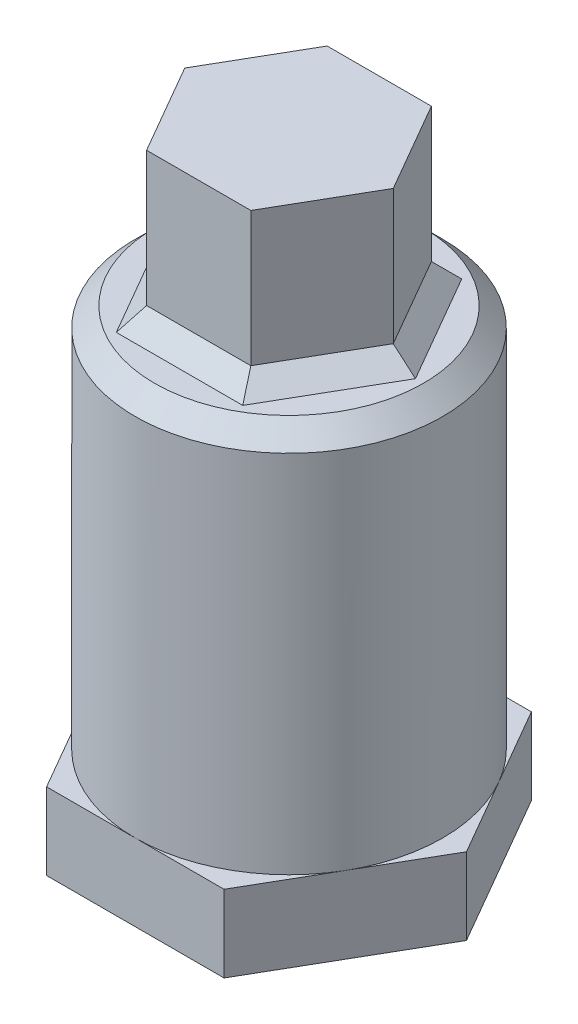
SolidWorks part; units mm, degrees
ref_plane "Front Plane" through (0, 0, 0) normal (0, 0, 1) x (1, 0, 0)
ref_plane "Top Plane" through (0, 0, 0) normal (0, 1, 0) x (1, 0, 0)
ref_plane "Right Plane" through (0, 0, 0) normal (1, 0, 0) x (0, 0, -1)
sketch "Sketch1" plane through (0, 0, 0) normal (0, 1, 0) x (1, 0, 0)
  line L1 (5.4271, 0) -> (2.7135, 4.7)
  line L2 (2.7135, 4.7) -> (-2.7135, 4.7)
  line L3 (-2.7135, 4.7) -> (-5.4271, 0)
  line L4 (-5.4271, 0) -> (-2.7135, -4.7)
  line L5 (-2.7135, -4.7) -> (2.7135, -4.7)
  line L6 (2.7135, -4.7) -> (5.4271, 0)
  circle A0 centre (0, 0) radius 4.7 construction
  dimension "D1" = 9.4
extrude "Boss-Extrude1" add sketch "Sketch1" along normal blind 8
sketch "Sketch2" plane through (0, 0, 0) normal (0, -1, 0) x (1, 0, 0)
  circle A0 centre (0, 0) radius 8
  dimension "D1" = 16
extrude "Boss-Extrude2" add sketch "Sketch2" along normal blind 20
chamfer "Chamfer1" distance 1 angle 45 7 edges at (0, 0, -8) (4.0703, 0, -2.35) (0, 0, -4.7) (-4.0703, 0, -2.35) (-4.0703, 0, 2.35) (0, 0, 4.7) (4.0703, 0, 2.35)
sketch "Sketch3" plane through (0, -20, 0) normal (0, -1, 0) x (1, 0, 0)
  circle A0 centre (0, 0) radius 23
  circle A1 centre (0, 0) radius 8 construction
  dimension "D1" = 15
extrude "Boss-Extrude3" add sketch "Sketch3" along normal blind 7
sketch "Sketch4" plane through (0, -27, 0) normal (0, -1, 0) x (1, 0, 0)
  line L1 (4.4, 0) -> (-4.4, 0) construction
  arc A0 (-24.8365, -2.8544) -> (-24.8365, 2.8544) centre (0, 0) cw construction
  arc A2 (-28.876, -2.6786) -> (-28.876, 2.6786) centre (0, 0) cw
  arc A3 (-28.8104, -3.3111) -> (-28.8104, 3.3111) centre (0, 0) cw construction
  spline S0 degree 3 poles (-28.876, 2.6786) (-27.341, 2.7837) (-21.4523, 3.0394) (-17.8705, 2.2022) (-15.9721, 0.5752) (-15.3766, 0) knots -0.203879 -0.203879 -0.203879 -0.203879 0 0.695602 1 1 1 1
  spline S1 degree 3 poles (-28.876, -2.6786) (-27.341, -2.7837) (-21.4523, -3.0394) (-17.8705, -2.2022) (-15.9721, -0.5752) (-15.3766, 0) knots -0.203879 -0.203879 -0.203879 -0.203879 0 0.695602 1 1 1 1
  point P11 (0, 0)
  dimension "D1" = 4
extrude "Cut-Extrude1" cut sketch "Sketch4" against normal blind 1 draft 45
fillet "Fillet2" radius 1 5 edges at (-22.8819, -26.5002, -2.3277) (-22.9013, -26.3001, 2.1282) (-23, -26, 0) (-18.9133, -26, 1.1779) (-21.1533, -26, -1.6856)
pattern_circular "CirPattern1" count 6 every 45 about axis through (0, -27, 0) along (0, 1, 0) of "Cut-Extrude1", "Fillet2"
sketch "Sketch5" plane through (0, -27, 0) normal (0, -1, 0) x (1, 0, 0)
  line L0 (-245.0554, -113.5226) -> (-245.0554, 81.9035) construction
  line L1 (0, -4.4) -> (0, 4.4) construction
  line L2 (-2.4074, -8.5668) -> (0, -10.6858)
  line L3 (0, 0.7457) -> (0, -10.6858) construction
  line L4 (2.4074, -8.5668) -> (0, -10.6858)
  spline S0 degree 1 poles (0, 0.7457) (-1.3665, 0.4718) knots 0 0 1 1
  spline S1 degree 1 poles (-1.3665, 0.4718) (-1.3494, -3.2772) knots 0 0 1 1
  spline S2 degree 3 poles (-1.3494, -3.2772) (-1.3228, -3.6344) (-1.1267, -4.1271) (-0.5986, -4.7724) (-0.2808, -5.1322) (0, -5.2972) knots 0 0 0 0 0.426063 0.616527 1 1 1 1
  spline S3 degree 3 poles (0, -6.811) (-0.5392, -6.4577) (-1.5601, -5.8942) (-2.516, -4.9333) (-2.9812, -4.1673) (-3.0132, -3.6202) (-3.016, -2.9456) (-2.9244, -2.1331) (-2.9103, -1.235) (-2.9092, -0.5693) (-2.9169, -0.011) (-3.1423, 0.6239) (-3.9909, 1.3241) (-5.2481, 2.0904) (-7.1532, 3.0787) (-8.9464, 3.8242) (-10.0759, 4.9012) (-10.5938, 5.8364) (-10.9217, 7.5348) (-10.9529, 8.9951) (-10.8334, 9.9239) knots 0 0 0 0 0.087818 0.156578 0.182085 0.206742 0.229318 0.273952 0.31724 0.351103 0.364287 0.392873 0.438837 0.509184 0.593709 0.730008 0.768263 0.802813 0.873163 1 1 1 1
  spline S4 degree 3 poles (-10.8334, 9.9239) (-11.243, 8.989) (-11.5419, 7.2897) (-11.6073, 5.0204) (-10.8157, 3.4928) (-9.6001, 2.669) (-8.1759, 1.7345) (-6.8872, 0.7533) (-5.7466, -0.2777) (-4.9296, -1.2509) (-4.9868, -2.1695) (-5.0027, -2.5385) knots 0 0 0 0 0.195889 0.33973 0.432671 0.517106 0.622276 0.767275 0.830917 0.925849 1 1 1 1
  spline S5 degree 3 poles (-5.0027, -2.5385) (-5.0233, -2.9907) (-5.3087, -3.4748) (-5.458, -4.4324) (-4.9971, -4.887) (-4.6741, -5.0396) knots 0 0 0 0 0.464937 0.585419 1 1 1 1
  spline S6 degree 3 poles (-4.6741, -5.0396) (-4.4706, -5.1519) (-3.98, -5.6073) (-3.2765, -6.1305) (-2.738, -6.7386) (-2.5993, -7.1771) (-2.6139, -7.784) (-2.7415, -8.3109) (-2.4074, -8.5668) knots 0 0 0 0 0.15475 0.447524 0.589127 0.691519 0.745256 1 1 1 1
  spline S7 degree 1 poles (0, 0.7457) (1.3665, 0.4718) knots 0 0 1 1
  spline S8 degree 1 poles (1.3665, 0.4718) (1.3494, -3.2772) knots 0 0 1 1
  spline S9 degree 3 poles (1.3494, -3.2772) (1.3228, -3.6344) (1.1267, -4.1271) (0.5986, -4.7724) (0.2808, -5.1322) (0, -5.2972) knots 0 0 0 0 0.426063 0.616527 1 1 1 1
  spline S10 degree 3 poles (0, -6.811) (0.5392, -6.4577) (1.5601, -5.8942) (2.516, -4.9333) (2.9812, -4.1673) (3.0132, -3.6202) (3.016, -2.9456) (2.9244, -2.1331) (2.9103, -1.235) (2.9092, -0.5693) (2.9169, -0.011) (3.1423, 0.6239) (3.9909, 1.3241) (5.2481, 2.0904) (7.1532, 3.0787) (8.9464, 3.8242) (10.0759, 4.9012) (10.5938, 5.8364) (10.9217, 7.5348) (10.9529, 8.9951) (10.8334, 9.9239) knots 0 0 0 0 0.087818 0.156578 0.182085 0.206742 0.229318 0.273952 0.31724 0.351103 0.364287 0.392873 0.438837 0.509184 0.593709 0.730008 0.768263 0.802813 0.873163 1 1 1 1
  spline S11 degree 3 poles (10.8334, 9.9239) (11.243, 8.989) (11.5419, 7.2897) (11.6073, 5.0204) (10.8157, 3.4928) (9.6001, 2.669) (8.1759, 1.7345) (6.8872, 0.7533) (5.7466, -0.2777) (4.9296, -1.2509) (4.9868, -2.1695) (5.0027, -2.5385) knots 0 0 0 0 0.195889 0.33973 0.432671 0.517106 0.622276 0.767275 0.830917 0.925849 1 1 1 1
  spline S12 degree 3 poles (5.0027, -2.5385) (5.0233, -2.9907) (5.3087, -3.4748) (5.458, -4.4324) (4.9971, -4.887) (4.6741, -5.0396) knots 0 0 0 0 0.464937 0.585419 1 1 1 1
  spline S13 degree 3 poles (4.6741, -5.0396) (4.4706, -5.1519) (3.98, -5.6073) (3.2765, -6.1305) (2.738, -6.7386) (2.5993, -7.1771) (2.6139, -7.784) (2.7415, -8.3109) (2.4074, -8.5668) knots 0 0 0 0 0.15475 0.447524 0.589127 0.691519 0.745256 1 1 1 1
  text T0 "B.o.B" font "Steamwreck" height in points 30
extrude "Cut-Extrude2" cut sketch "Sketch5" against normal blind 1
sketch "Sketch7" plane through (0, -20, 0) normal (0, 1, 0) x (1, 0, 0)
  circle A0 centre (0, 0) radius 24.8704
extrude "Cut-Extrude3" cut sketch "Sketch7" against normal through all
sketch "Sketch8" plane through (0, -20, 0) normal (0, -1, 0) x (1, 0, 0)
  line L1 (9.2376, 0) -> (4.6188, 8)
  line L2 (4.6188, 8) -> (-4.6188, 8)
  line L3 (-4.6188, 8) -> (-9.2376, 0)
  line L4 (-9.2376, 0) -> (-4.6188, -8)
  line L5 (-4.6188, -8) -> (4.6188, -8)
  line L6 (4.6188, -8) -> (9.2376, 0)
  circle A0 centre (0, 0) radius 8 construction
  dimension "D1" = 16
extrude "Boss-Extrude10" add sketch "Sketch8" along normal blind 4 contours L4 L5 L6 L1 L2 L3
